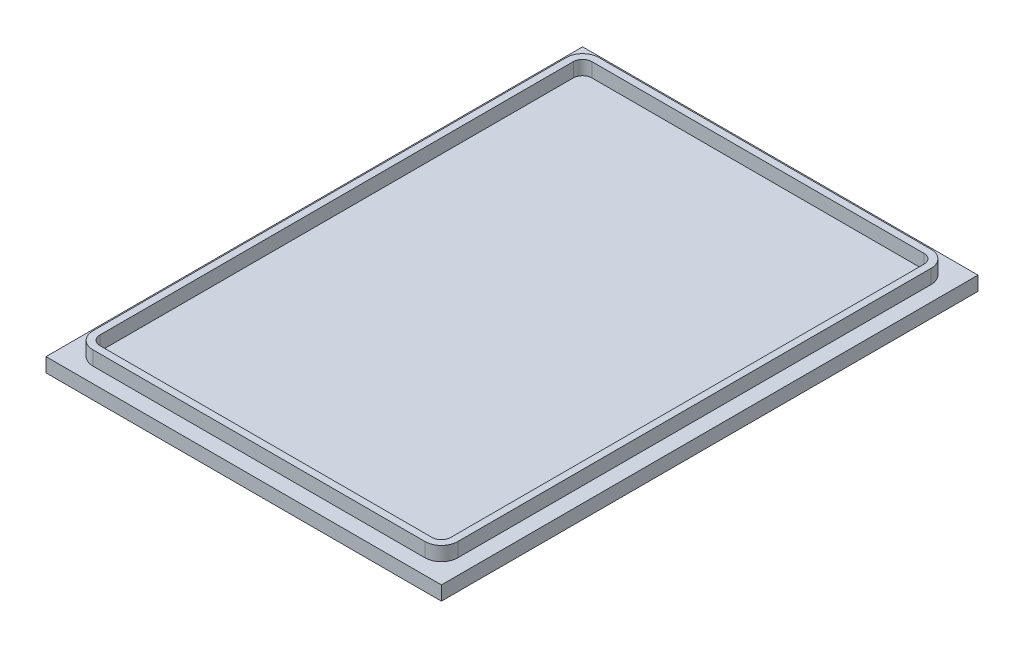
SolidWorks part; units mm, degrees
material "6061-T6 (SS)"
ref_plane "Front Plane" through (0, 0, 0) normal (0, 0, 1) x (1, 0, 0)
ref_plane "Top Plane" through (0, 0, 0) normal (0, 1, 0) x (1, 0, 0)
ref_plane "Right Plane" through (0, 0, 0) normal (1, 0, 0) x (0, 0, -1)
sketch "Sketch1" plane through (0, 0, 0) normal (0, 1, 0) x (1, 0, 0)
  line L1 (-44.45, 60.325) -> (44.45, 60.325)
  line L2 (-44.45, 60.325) -> (-44.45, -60.325)
  line L3 (-44.45, -60.325) -> (44.45, -60.325)
  line L4 (44.45, 60.325) -> (44.45, -60.325)
  line L5 (-44.45, 60.325) -> (44.45, -60.325) construction
  line L6 (-44.45, -60.325) -> (44.45, 60.325) construction
  point P0 (0, 0)
  dimension "D1" = 88.9
  dimension "D2" = 120.65
extrude "Boss-Extrude1" add sketch "Sketch1" along normal blind 3.175
sketch "Sketch2" plane through (0, 3.175, 0) normal (0, 1, 0) x (1, 0, 0)
  line L0 (44.45, 60.325) -> (-44.45, 60.325) construction
  line L1 (-37.338, 56.896) -> (37.338, 56.896)
  line L2 (-41.021, 53.213) -> (-41.021, -53.213)
  line L3 (-37.338, -56.896) -> (37.338, -56.896)
  line L4 (41.021, 53.213) -> (41.021, -53.213)
  line L5 (-41.021, 56.896) -> (41.021, -56.896) construction
  line L6 (-41.021, -56.896) -> (41.021, 56.896) construction
  line L7 (-44.45, 60.325) -> (-44.45, -60.325) construction
  arc A0 (-41.021, -53.213) -> (-37.338, -56.896) centre (-37.338, -53.213) ccw
  arc A1 (37.338, -56.896) -> (41.021, -53.213) centre (37.338, -53.213) ccw
  arc A2 (37.338, 56.896) -> (41.021, 53.213) centre (37.338, 53.213) cw
  arc A3 (-37.338, 56.896) -> (-41.021, 53.213) centre (-37.338, 53.213) ccw
  point P0 (0, 0)
  dimension "D1" = 3.683
  dimension "D2" = 3.429
  dimension "D3" = 3.429
extrude "Boss-Extrude2" add sketch "Sketch2" along normal blind 3.175
sketch "Sketch3" plane through (0, 6.35, 0) normal (0, 1, 0) x (1, 0, 0)
  line L0 (-37.338, -56.896) -> (37.338, -56.896) construction
  line L1 (41.021, -53.213) -> (41.021, 53.213) construction
  line L2 (-41.021, 53.213) -> (-41.021, -53.213) construction
  line L3 (37.338, 56.896) -> (-37.338, 56.896) construction
  line L4 (-37.338, -56.896) -> (37.338, -56.896) construction
  line L5 (41.021, -53.213) -> (41.021, 53.213) construction
  line L6 (-41.021, 53.213) -> (-41.021, -53.213) construction
  line L7 (37.338, 56.896) -> (-37.338, 56.896) construction
  line L8 (-37.338, -55.3085) -> (37.338, -55.3085)
  line L9 (39.4335, -53.213) -> (39.4335, 53.213)
  line L10 (37.338, 55.3085) -> (-37.338, 55.3085)
  line L11 (-39.4335, 53.213) -> (-39.4335, -53.213)
  arc A0 (-41.021, -53.213) -> (-37.338, -56.896) centre (-37.338, -53.213) ccw construction
  arc A1 (37.338, -56.896) -> (41.021, -53.213) centre (37.338, -53.213) ccw construction
  arc A2 (41.021, 53.213) -> (37.338, 56.896) centre (37.338, 53.213) ccw construction
  arc A3 (-37.338, 56.896) -> (-41.021, 53.213) centre (-37.338, 53.213) ccw construction
  arc A4 (-41.021, -53.213) -> (-37.338, -56.896) centre (-37.338, -53.213) ccw construction
  arc A5 (37.338, -56.896) -> (41.021, -53.213) centre (37.338, -53.213) ccw construction
  arc A6 (41.021, 53.213) -> (37.338, 56.896) centre (37.338, 53.213) ccw construction
  arc A7 (-37.338, 56.896) -> (-41.021, 53.213) centre (-37.338, 53.213) ccw construction
  arc A8 (37.338, -55.3085) -> (39.4335, -53.213) centre (37.338, -53.213) ccw
  arc A9 (39.4335, 53.213) -> (37.338, 55.3085) centre (37.338, 53.213) ccw
  arc A10 (-37.338, 55.3085) -> (-39.4335, 53.213) centre (-37.338, 53.213) ccw
  arc A11 (-39.4335, -53.213) -> (-37.338, -55.3085) centre (-37.338, -53.213) ccw
  dimension "D1" = 1.5875
extrude "Cut-Extrude1" cut sketch "Sketch3" against normal blind 3.175
